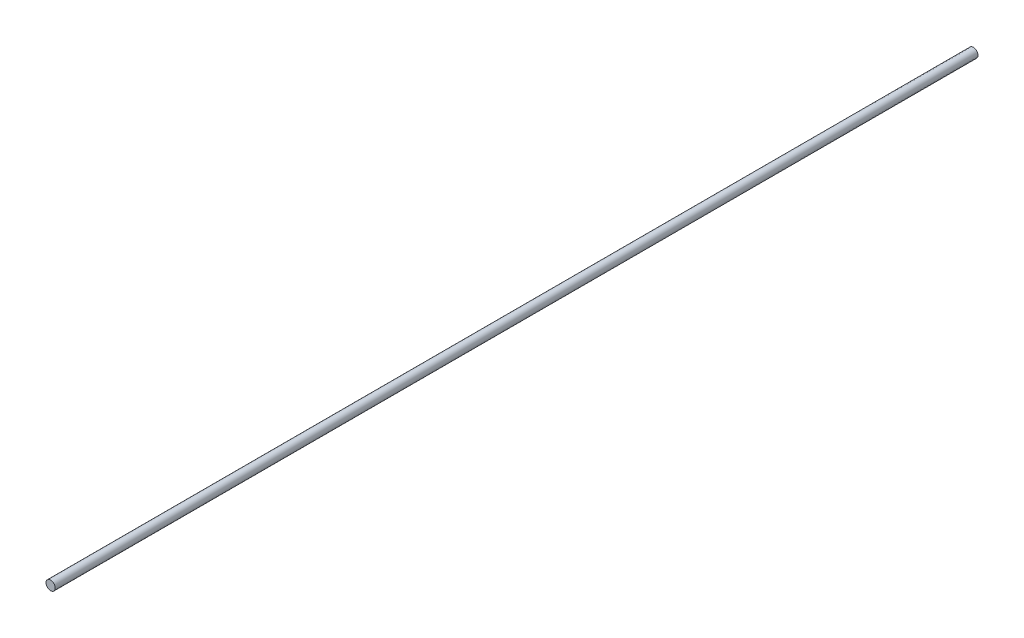
SolidWorks part; units mm, degrees
material "6061-T6 (SS)"
ref_plane "Front Plane" through (0, 0, 0) normal (0, 0, 1) x (1, 0, 0)
ref_plane "Top Plane" through (0, 0, 0) normal (0, 1, 0) x (1, 0, 0)
ref_plane "Right Plane" through (0, 0, 0) normal (1, 0, 0) x (0, 0, -1)
sketch "Sketch1" plane through (0, 0, 0) normal (0, 0, 1) x (1, 0, 0)
  line L1 (-1.905, 0) -> (1.905, 0) construction
  dimension "OD" = 3.81
sketch "Sketch2" plane through (0, 0, 0) normal (1, 0, 0) x (0, 0, -1)
  line L0 (190.5, 0) -> (-190.5, 0)
  point P0 (-142.875, 0)
  point P3 (142.875, 0)
  point P4 (0, 0)
  dimension "Length" = 381
  dimension "D1" = 47.625
  dimension "D2" = 47.625
sketch "Sketch3" plane through (0, 0, 0) normal (0, 0, 1) x (1, 0, 0)
  circle A0 centre (0, 0) radius 1.905
extrude "Boss-Extrude1" add sketch "Sketch3" along normal up to vertex (190.5 mm away) and the other way up to vertex (190.5 mm away) up to point (0, 0, 190.5) other way up to point (0, 0, -190.5)
equation "\"D1@Sketch2\"=\"Length@Sketch2\"/8"
equation "\"D2@Sketch2\"=\"D1@Sketch2\""
